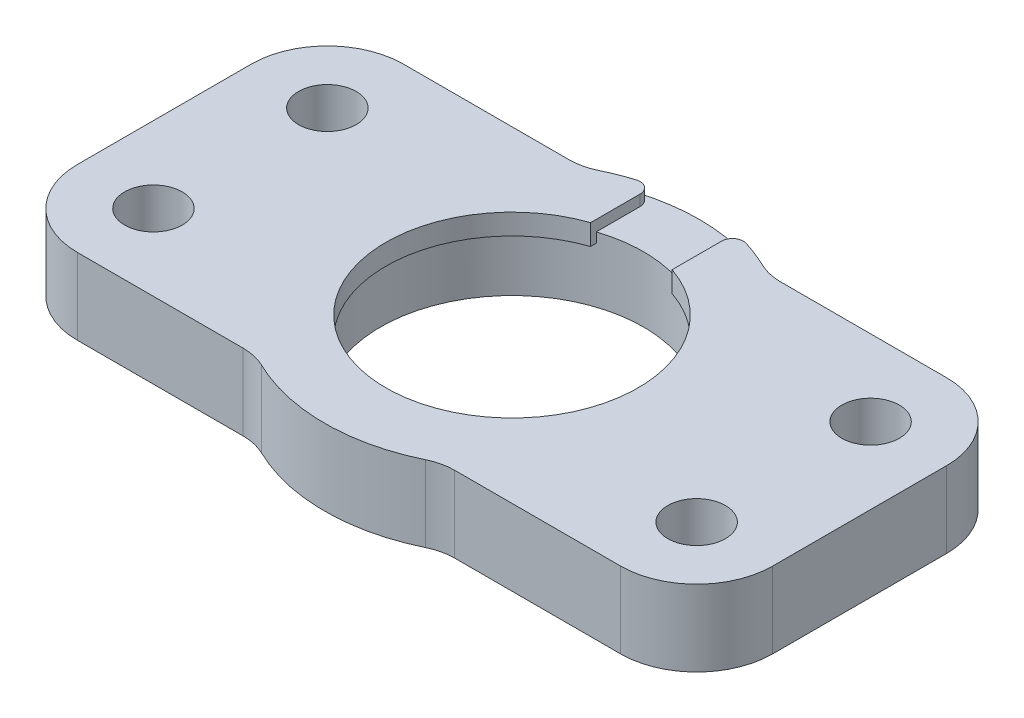
SolidWorks part; units mm, degrees
ref_plane "前视基准面" through (0, 0, 0) normal (0, 0, 1) x (1, 0, 0)
ref_plane "上视基准面" through (0, 0, 0) normal (0, 1, 0) x (1, 0, 0)
ref_plane "右视基准面" through (0, 0, 0) normal (1, 0, 0) x (0, 0, -1)
other "Configuration Table"
sketch "草图2" plane through (0, 0, 0) normal (0, 1, 0) x (1, 0, 0)
  line L0 (0, 0) -> (9.4021, 0) construction
  line L1 (0, 0) -> (0, -6.8504) construction
  line L2 (33.4831, -23) -> (49.97, -23)
  line L3 (24.985, -16) -> (24.985, -8.9065) construction
  line L4 (0, 7) -> (16.4869, 7)
  line L5 (-7, 0) -> (-7, -16)
  line L6 (0, -23) -> (16.4869, -23)
  line L7 (56.97, 0) -> (56.97, -16)
  line L8 (33.4831, 7) -> (49.97, 7)
  circle A0 centre (0, 0) radius 2.65
  circle A1 centre (0, -16) radius 2.65
  circle A2 centre (49.97, 0) radius 2.65
  circle A3 centre (49.97, -16) radius 2.65
  arc A4 (49.97, -23) -> (56.97, -16) centre (49.97, -16) ccw
  arc A5 (56.97, 0) -> (49.97, 7) centre (49.97, 0) ccw
  arc A6 (0, -23) -> (-7, -16) centre (0, -16) cw
  arc A7 (-7, 0) -> (0, 7) centre (0, 0) cw
  arc A8 (16.4869, -23) -> (33.4831, -23) centre (24.985, -8) ccw
  circle A9 centre (24.985, -8) radius 12.1
  arc A10 (33.4831, 7) -> (16.4869, 7) centre (24.985, -8) ccw
  dimension "D1" = 5.3
  dimension "D4" = 14
  dimension "D6" = 34.48
  dimension "D7" = 24.2
  dimension "D2" = 16
  dimension "D3" = 49.97
  dimension "D5" = 8
extrude "凸台-拉伸1" add sketch "草图2" along normal blind 7
sketch "草图3" plane through (0, 7, 0) normal (0, 1, 0) x (1, 0, 0)
  circle A0 centre (24.985, -8) radius 12.1 construction
  circle A1 centre (24.985, -8) radius 12.1
  circle A2 centre (24.985, -8) radius 11.6
  dimension "D1" = 23.2
extrude "凸台-拉伸2" add sketch "草图3" against normal blind 1.9
fillet "圆角1" radius 5 4 edges at (33.4831, 3.5, 23) (16.4869, 3.5, 23) (33.4831, 3.5, -7) (16.4869, 3.5, -7)
sketch "草图5" plane through (0, 7, 0) normal (0, 1, 0) x (1, 0, 0)
  line L0 (24.985, -8) -> (24.985, 17) construction
  line L1 (21.235, 8.8272) -> (21.235, 2.9771)
  line L2 (28.735, 8.8272) -> (28.735, 2.9771)
  circle A0 centre (24.985, -8) radius 11.6 construction
  arc A1 (32.5253, 7.5036) -> (17.4447, 7.5036) centre (24.985, -8) ccw construction
  arc A2 (28.735, 2.9771) -> (21.235, 2.9771) centre (24.985, -8) ccw
  arc A3 (28.735, 8.8272) -> (21.235, 8.8272) centre (24.985, -8) ccw
  dimension "D1" = 7.5
extrude "切除-拉伸2" cut sketch "草图5" against normal blind 1
sketch "草图6" plane through (0, 6, 0) normal (0, 1, 0) x (1, 0, 0)
  line L0 (28.735, 2.9771) -> (28.735, 8.8272) construction
  line L1 (21.235, 8.8272) -> (21.235, 2.9771) construction
  line L2 (28.735, 2.9771) -> (28.735, 3.5042)
  line L3 (21.235, 3.5042) -> (21.235, 2.9771)
  arc A0 (28.735, 3.5042) -> (21.235, 3.5042) centre (24.985, -8) ccw
  arc A1 (28.735, 2.9771) -> (21.235, 2.9771) centre (24.985, -8) ccw
  dimension "D1" = 24.2
extrude "切除-拉伸3" cut sketch "草图6" against normal through all
fillet "圆角3" radius 1 2 edges at (21.235, 6.5, -8.8272) (28.735, 6.5, -8.8272)
